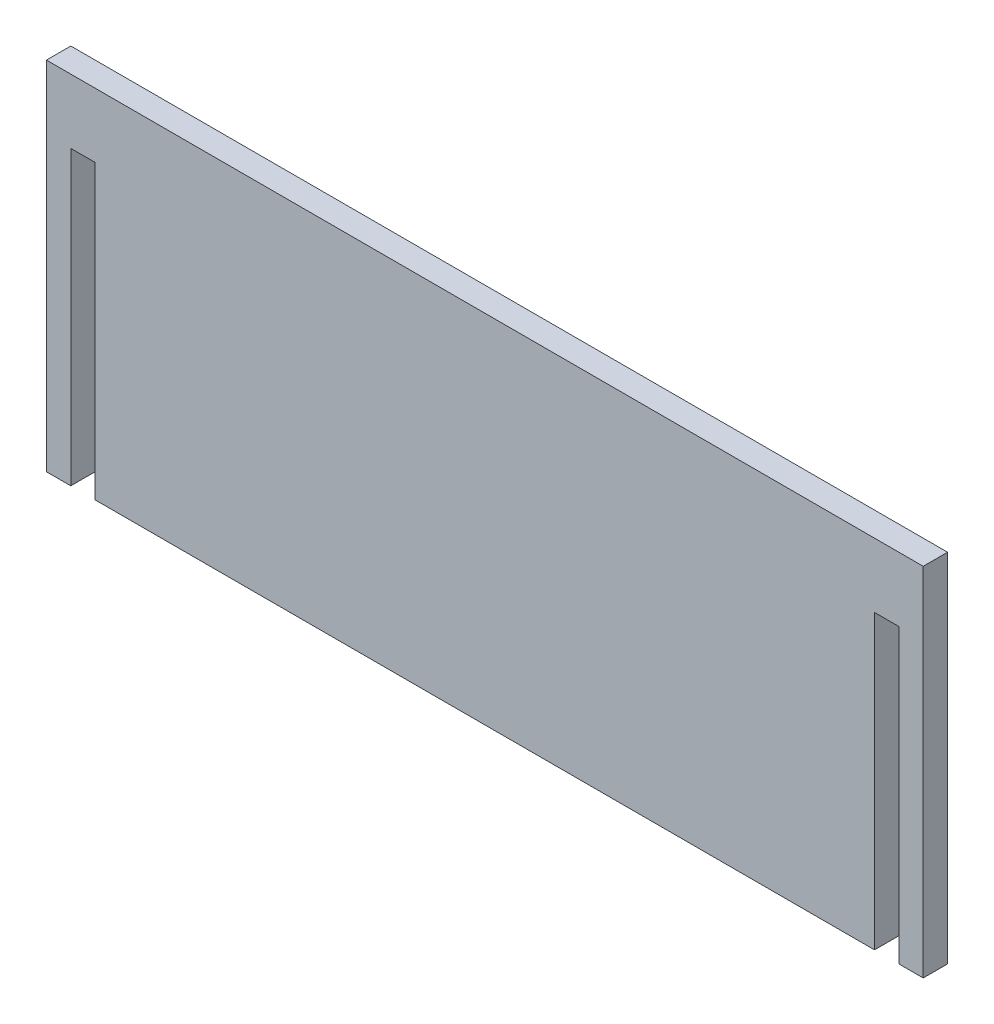
SolidWorks part; units mm, degrees
ref_plane "Front Plane" through (0, 0, 0) normal (0, 0, 1) x (1, 0, 0)
ref_plane "Top Plane" through (0, 0, 0) normal (0, 1, 0) x (1, 0, 0)
ref_plane "Right Plane" through (0, 0, 0) normal (1, 0, 0) x (0, 0, -1)
sketch "Sketch1" plane through (0, 0, 0) normal (0, 0, 1) x (1, 0, 0)
  line L1 (0, 0) -> (114.3, 0)
  line L2 (0, 0) -> (0, 46.482)
  line L3 (0, 46.482) -> (114.3, 46.482)
  line L4 (114.3, 0) -> (114.3, 46.482)
  dimension "D1" = 114.3
  dimension "D2" = 46.482
extrude "Boss-Extrude1" add sketch "Sketch1" along normal blind 3.175
sketch "Sketch2" plane through (0, 0, 3.175) normal (0, 0, 1) x (1, 0, 0)
  line L0 (0, 0) -> (114.3, 0) construction
  line L1 (3.175, 0) -> (6.35, 0)
  line L2 (3.175, 0) -> (3.175, 38.1)
  line L3 (3.175, 38.1) -> (6.35, 38.1)
  line L4 (6.35, 0) -> (6.35, 38.1)
  line L5 (57.15, 46.482) -> (57.15, 0) construction
  line L6 (114.3, 46.482) -> (0, 46.482) construction
  line L7 (0, 46.482) -> (0, 0) construction
  line L8 (111.125, 0) -> (107.95, 0)
  line L9 (107.95, 0) -> (107.95, 38.1)
  line L10 (111.125, 38.1) -> (107.95, 38.1)
  line L11 (111.125, 0) -> (111.125, 38.1)
  dimension "D1" = 3.175
  dimension "D2" = 3.175
  dimension "D3" = 38.1
extrude "Cut-Extrude1" cut sketch "Sketch2" against normal through all
